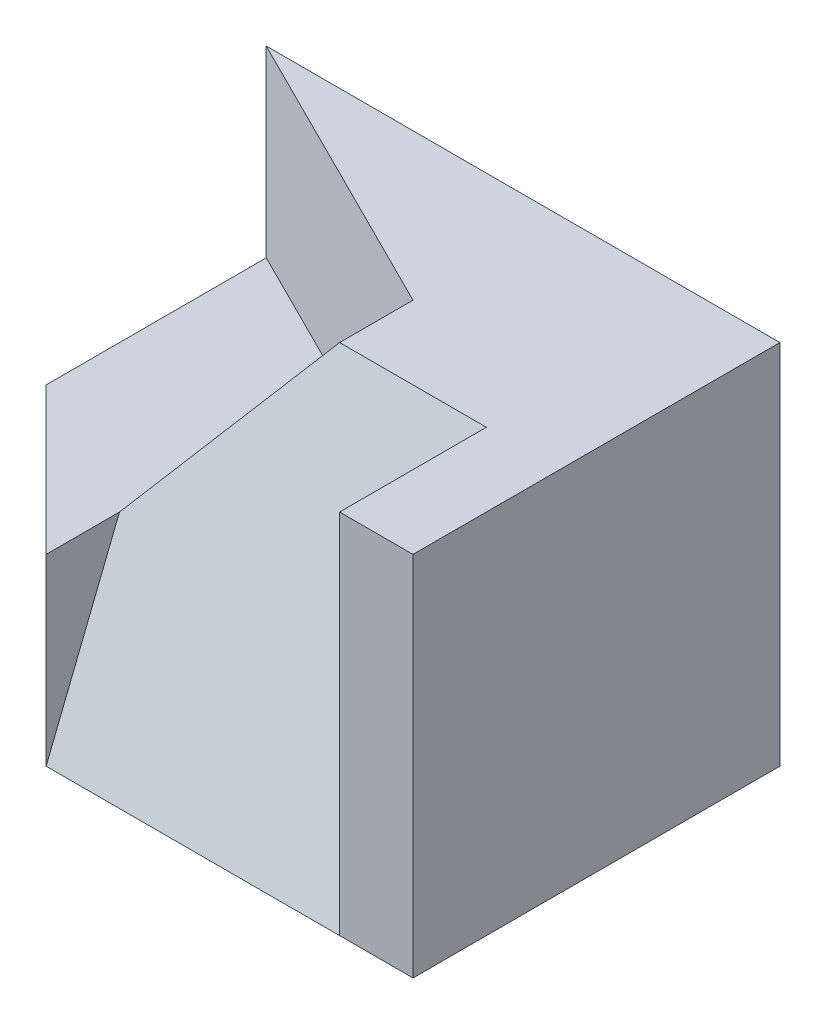
SolidWorks part; units mm, degrees
ref_plane "Front Plane" through (0, 0, 0) normal (0, 0, 1) x (1, 0, 0)
ref_plane "Top Plane" through (0, 0, 0) normal (0, 1, 0) x (1, 0, 0)
ref_plane "Right Plane" through (0, 0, 0) normal (1, 0, 0) x (0, 0, -1)
sketch "Sketch1" plane through (0, 0, 0) normal (0, 0, 1) x (1, 0, 0)
  line L1 (0, 0) -> (70, 0)
  line L2 (0, 0) -> (0, 50)
  line L3 (0, 50) -> (70, 50)
  line L4 (70, 0) -> (70, 50)
  dimension "D1" = 70
  dimension "D2" = 50
extrude "Boss-Extrude1" add sketch "Sketch1" along normal blind 50
sketch "Sketch2" plane through (0, 0, 0) normal (0, -1, 0) x (1, 0, 0)
  line L0 (0, 30) -> (20, 50)
  line L1 (0, 50) -> (0, 0) construction
  line L2 (0, 50) -> (70, 50) construction
  line L3 (20, 50) -> (0, 50)
  line L4 (0, 50) -> (0, 30)
  dimension "D1" = 20
  dimension "D2" = 20
extrude "Cut-Extrude1" cut sketch "Sketch2" against normal blind 50
sketch "Sketch3" plane through (0, 0, 50) normal (0, 0, 1) x (1, 0, 0)
  line L0 (60, 0) -> (60, 50)
  line L1 (20, 0) -> (70, 0) construction
  line L2 (70, 50) -> (20, 50) construction
  line L3 (60, 50) -> (40, 50)
  line L4 (40, 50) -> (20, 30)
  line L5 (20, 50) -> (20, 0) construction
  line L6 (20, 30) -> (20, 0)
  line L7 (20, 0) -> (60, 0)
  dimension "D1" = 20
  dimension "D2" = 10
  dimension "D3" = 20
extrude "Cut-Extrude2" cut sketch "Sketch3" against normal blind 20
sketch "Sketch4" plane through (0, 50, 0) normal (0, 1, 0) x (1, 0, 0)
  line L0 (40, -30) -> (40, -20)
  line L1 (40, -20) -> (0, 0)
  line L2 (0, 0) -> (0, -30)
  line L3 (0, -30) -> (20, -50)
  line L4 (20, -50) -> (40, -50)
  line L5 (40, -50) -> (40, -30)
  line L6 (40, -30) -> (20, -50)
  line M14 (0, 0) -> (0, -30)
  line M15 (0, -30) -> (20, -50)
  dimension "D1" = 10
extrude "Cut-Extrude3" cut sketch "Sketch4" against normal blind 20 contours L6 L0 L1 M14 M15
sketch "Sketch5" plane through (0, 30, 0) normal (0, 1, 0) x (1, 0, 0)
  line L0 (0, 0) -> (0, -30)
  line L1 (0, -30) -> (20, -50)
  line L2 (20, -50) -> (20, -30)
  line L3 (20, -30) -> (40, -30)
  line L4 (40, -30) -> (40, -20)
  line L5 (40, -20) -> (0, 0)
extrude "Cut-Extrude4" cut sketch "Sketch5" against normal blind 5
sketch "Sketch6" plane through (0, 25, 0) normal (0, 1, 0) x (1, 0, 0)
  line L0 (20, -30) -> (20, -10)
  line L1 (40, -20) -> (0, 0) construction
  line L2 (20, -10) -> (40, -20)
  line L3 (40, -20) -> (40, -30)
  line L4 (40, -30) -> (20, -30)
  line L5 (20, -30) -> (19.8875, -30.3601)
  line M1 (40, -20) -> (0, 0)
  line M5 (20, -30) -> (40, -30)
  line M6 (40, -30) -> (40, -20)
extrude "Boss-Extrude2" add sketch "Sketch6" along normal blind 25 contours L0 M5 M6 M1
sketch "Sketch7" plane through (0, 50, 0) normal (0, 1, 0) x (1, 0, 0)
  line L0 (20, -50) -> (40, -50)
  line L1 (40, -50) -> (40, -30)
  line L2 (60, -30) -> (20, -30) construction
  line L3 (40, -30) -> (20, -50)
extrude "Cut-Extrude5" cut sketch "Sketch7" against normal blind 25
sketch "Sketch8" plane through (0, 0, 0) normal (0, -1, 0) x (1, 0, 0)
  line L0 (20, 50) -> (20, 40)
  line L1 (20, 30) -> (20, 50) construction
  line L2 (20, 40) -> (40, 30)
  line L3 (20, 30) -> (60, 30) construction
  line L4 (40, 30) -> (60, 30)
  line L5 (60, 30) -> (60, 50)
  line L6 (60, 50) -> (20, 50)
  dimension "D1" = 20
extrude "Boss-Extrude3" add sketch "Sketch8" against normal blind 30
sketch "Sketch9" plane through (0, 50, 0) normal (0, 1, 0) x (1, 0, 0)
  line L0 (40, -30) -> (40, -20)
  line L1 (60, -30) -> (20, -30) construction
  line L2 (40, -20) -> (20, -10)
  line L3 (20, -10) -> (20, -40)
  line L4 (20, -40) -> (40, -30)
  line L5 (40, -30) -> (20, -30)
  line L6 (20, -30) -> (40, -30)
  line M4 (20, -30) -> (60, -30)
  dimension "D1" = 10
  dimension "D2" = 10
extrude "Boss-Extrude4" add sketch "Sketch9" against normal blind 50 contours L3 L4 M4
sketch "Sketch10" plane through (0, 50, 0) normal (0, 1, 0) x (1, 0, 0)
  line L0 (20, -40) -> (40, -30)
  line L1 (40, -30) -> (40, -20)
  line L2 (40, -20) -> (20, -10)
  line L3 (20, -10) -> (20, -40)
  dimension "D1" = 10
extrude "Cut-Extrude7" cut sketch "Sketch10" against normal blind 15
ref_plane "Plane1" through (0, 17.2414, 43.1034) normal (0, 0.3714, 0.9285) x (1, 0, 0)
sketch "Sketch11" plane through (0, 17.2414, 43.1034) normal (0, 0.3714, 0.9285) x (1, 0, 0)
  line L0 (60, 35.2821) -> (60, -18.5695)
  line L1 (20, -18.5695) -> (70, -18.5695) construction
  line L2 (60, -18.5695) -> (20, -18.5695)
  line L3 (20, -18.5695) -> (20, 4.6424)
  line L4 (20, 4.6424) -> (40, 35.2821)
  line L5 (40, 35.2821) -> (60, 35.2821)
extrude "Cut-Extrude8" cut sketch "Sketch11" along normal blind 15
sketch "Sketch12" plane through (0, 17.2414, 43.1034) normal (0, 0.3714, 0.9285) x (1, 0, 0)
  line L0 (40, 35.2821) -> (60, 35.2821)
  line L1 (60, 35.2821) -> (60, -18.5695)
  line L2 (60, -18.5695) -> (20, -18.5695)
  line L3 (20, -18.5695) -> (20, 4.6424)
  line L4 (20, 4.6424) -> (40, 35.2821)
extrude "Boss-Extrude5" add sketch "Sketch12" against normal blind 15
sketch "Sketch13" plane through (11.8995, -7.2118, 2.8847) normal (0.8374, -0.5075, 0.203) x (0.1736, -0.1052, -0.9792)
  line L0 (-48.1172, 31.746) -> (-48.1172, 37.5926)
  line L1 (-48.1172, 37.5926) -> (-35.862, 39.1004)
  line L2 (-35.862, 39.1004) -> (-39.3132, 28.797)
  line L3 (-39.3132, 28.797) -> (-48.1172, 31.746)
extrude "Cut-Extrude12" cut sketch "Sketch13" against normal blind 15
sketch "Sketch15" plane through (0, 17.2414, 43.1034) normal (0, 0.3714, 0.9285) x (1, 0, 0)
  line L0 (40, 35.2821) -> (20, 35.2821)
  line L1 (20, 35.2821) -> (20, -18.5695)
  line L2 (40, 35.2821) -> (20, -18.5695)
extrude "Cut-Extrude13" cut sketch "Sketch15" along normal blind 15
sketch "Sketch16" plane through (0, 17.2414, 43.1034) normal (0, 0.3714, 0.9285) x (1, 0, 0)
  line L0 (24, 13.7415) -> (25.9394, 13.7415)
  line L1 (25.9394, 13.7415) -> (28, 19.1266)
  line L2 (28, 19.1266) -> (29.4545, 19.1266)
  line L3 (40, 35.2821) -> (25.9394, 13.7415) construction
  line L4 (29.4545, 19.1266) -> (25.9394, 13.7415)
  line L5 (25.9394, 13.7415) -> (25.9516, 13.6481)
  line M5 (40, 35.2821) -> (25.9394, 13.7415)
  line M6 (25.9394, 13.7415) -> (24, 13.7415)
  line M7 (24, 13.7415) -> (28, 19.1266)
extrude "Boss-Extrude6" add sketch "Sketch16" against normal blind 15 contours L1 M6 M7 | L2 L1 M5
ref_plane "Plane2" through (-7.9027, 7.2948, 2.4316) normal (0.7167, -0.6616, -0.2205) x (-0.162, 0.1496, -0.9754)
sketch "Sketch22" plane through (0, 0, 0) normal (0, -1, 0) x (-1, 0, 0)
  line L1 (0, 0) -> (-70, 0)
  line L2 (0, 0) -> (0, -50)
  line L3 (0, -50) -> (-70, -50)
  line L4 (-70, 0) -> (-70, -50)
extrude "Cut-Extrude15" cut sketch "Sketch22" along normal blind 15
ref_plane "Plane5" through (-9.6, 12.8, 0) normal (-0.6, 0.8, 0) x (0.8, 0.6, 0)
sketch "Sketch28" plane through (-9.6, 12.8, 0) normal (-0.6, 0.8, 0) x (0.8, 0.6, 0)
  line L0 (37, -36) -> (62, -30)
  line L1 (62, -30) -> (62, -20)
  line L2 (62, -20) -> (37, -10)
  line L3 (37, -10) -> (37, -36)
extrude "Boss-Extrude11" add sketch "Sketch28" against normal blind 15
ref_plane "Plane6" through (0, 0, 0) normal (0.7809, -0.6247, 0) x (0, 0, -1)
sketch "Sketch29" plane through (0, 0, 0) normal (0.7809, -0.6247, 0) x (0, 0, -1)
  line L0 (-40, 32.0156) -> (-30, 64.0312)
  line L1 (-30, 64.0312) -> (-20, 64.0312)
  line L2 (-20, 64.0312) -> (-10, 32.0156)
  line L3 (-10, 32.0156) -> (-40, 32.0156)
extrude "Cut-Extrude18" cut sketch "Sketch29" against normal blind 15
sketch "Sketch30" plane through (0, 0, 0) normal (-0.4472, 0, 0.8944) x (0.8944, 0, 0.4472)
  line L0 (0, 50) -> (44.7214, 50)
  line L1 (44.7214, 50) -> (22.3607, 25)
  line L2 (22.3607, 25) -> (0, 25)
  line L3 (0, 25) -> (0, 50)
extrude "Cut-Extrude19" cut sketch "Sketch30" along normal blind 15
sketch "Sketch32" plane through (0, 17.2414, 43.1034) normal (0, 0.3714, 0.9285) x (1, 0, 0)
  line L0 (28, 19.1266) -> (40, 35.2821)
  line L1 (40, 35.2821) -> (29.4545, 19.1266)
  line L2 (29.4545, 19.1266) -> (28, 19.1266)
extrude "Boss-Extrude14" add sketch "Sketch32" against normal blind 15
sketch "Sketch34" plane through (0, 25, 0) normal (0, 1, 0) x (1, 0, 0)
  line L0 (14.3103, -40) -> (20, -40)
  line L1 (20, -40) -> (20, -50)
  line L2 (20, -50) -> (14.3103, -40)
extrude "Boss-Extrude17" add sketch "Sketch34" against normal blind 25
sketch "Sketch35" plane through (0, 0, 0) normal (-0.7809, 0.6247, 0) x (0, 0, 1)
  line L0 (30, 64.0312) -> (40, 32.0156)
  line L1 (40, 32.0156) -> (10, 32.0156)
  line L2 (10, 32.0156) -> (20, 64.0312)
  line L3 (20, 64.0312) -> (30, 64.0312)
extrude "Boss-Extrude18" add sketch "Sketch35" against normal blind 25
